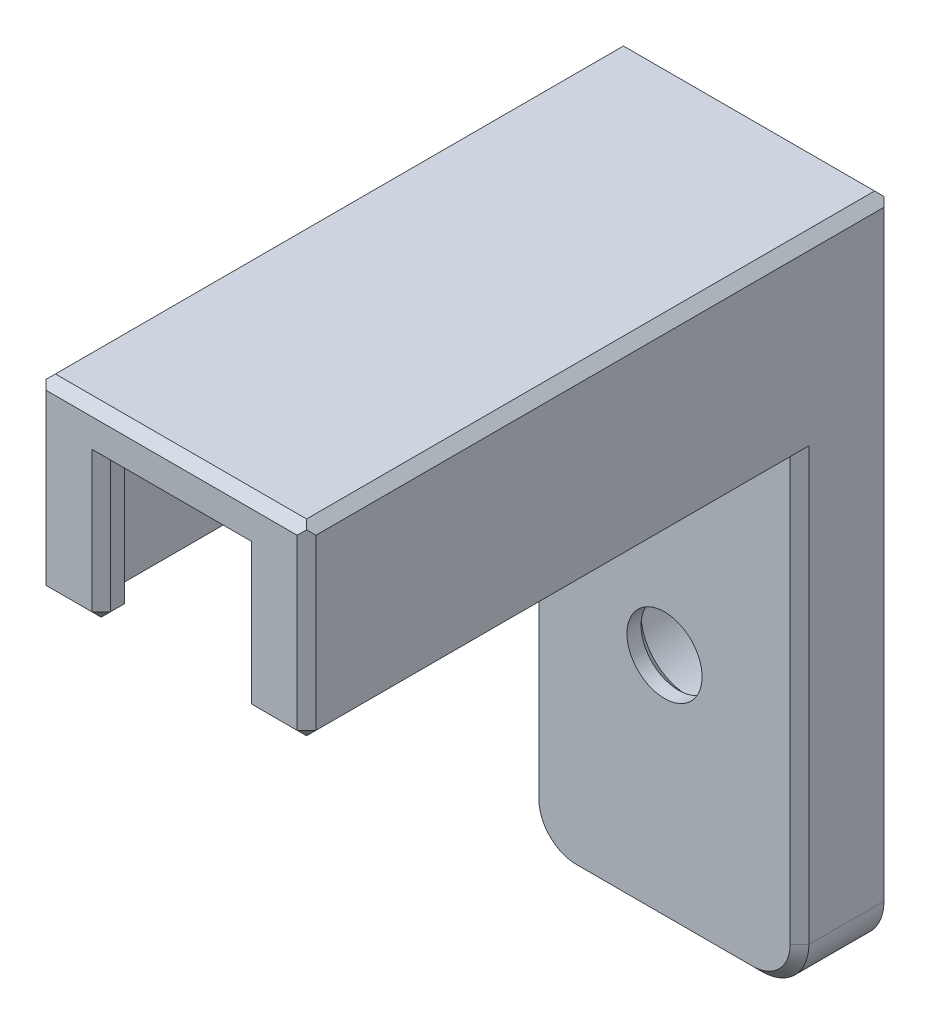
SolidWorks part; units mm, degrees
ref_plane "Front Plane" through (0, 0, 0) normal (0, 0, 1) x (1, 0, 0)
ref_plane "Top Plane" through (0, 0, 0) normal (0, 1, 0) x (1, 0, 0)
ref_plane "Right Plane" through (0, 0, 0) normal (1, 0, 0) x (0, 0, -1)
sketch "Sketch1" plane through (0, 0, 0) normal (0, 1, 0) x (1, 0, 0)
  line L1 (-5.75, 12.5) -> (5.75, 12.5)
  line L2 (-5.75, 12.5) -> (-5.75, -12.5)
  line L3 (-5.75, -12.5) -> (5.75, -12.5)
  line L4 (5.75, 12.5) -> (5.75, -12.5)
  point P4 (0, -12.5)
  point P6 (-5.75, 0)
  dimension "D1" = 25
  dimension "D2" = 11.5
extrude "Boss-Extrude1" add sketch "Sketch1" along normal blind 8
sketch "Sketch2" plane through (0, 0, 0) normal (0, -1, 0) x (1, 0, 0)
  line L0 (-5.75, 12.5) -> (5.75, 12.5) construction
  line L1 (-3, 12.5) -> (3, 12.5)
  line L2 (-3, 12.5) -> (-3, 11.5)
  line L4 (3, 12.5) -> (3, 11.5)
  line L5 (3, 11.5) -> (3.8, 11.5)
  line L6 (-3.8, 11.5) -> (-3, 11.5)
  line L7 (-3.8, 11.5) -> (-3.8, 4.5)
  line L8 (-3.8, 4.5) -> (-3, 4.5)
  line L9 (3.8, 11.5) -> (3.8, 4.5)
  line L10 (-3, 11.5) -> (3, 11.5) construction
  line L12 (3, 4.5) -> (3.8, 4.5)
  line L13 (-3, 4.5) -> (3, 4.5) construction
  line L14 (-3, 4.5) -> (-3, -2.5)
  line L15 (-3, -2.5) -> (3, -2.5)
  line L16 (3, 4.5) -> (3, -2.5)
  line L17 (-3, 4.5) -> (3, 4.5) construction
  point P10 (0, 12.5)
  point P13 (3.4, 11.5)
  dimension "D1" = 7.6
  dimension "D2" = 6
  dimension "D3" = 1
  dimension "D4" = 7
  dimension "D5" = 6
  dimension "D6" = 14
extrude "Cut-Extrude1" cut sketch "Sketch2" against normal offset from surface (6 mm away) 6 up to face at (0, 0, 0)
sketch "Sketch3" plane through (0, 0, 0) normal (0, -1, 0) x (1, 0, 0)
  line L0 (5.75, 12.5) -> (5.75, -12.5) construction
  line L1 (-5.75, -12.5) -> (5.75, -12.5)
  line L2 (-5.75, -12.5) -> (-5.75, -8.5)
  line L3 (-5.75, -8.5) -> (5.75, -8.5)
  line L4 (5.75, -12.5) -> (5.75, -8.5)
  line L5 (3.8, 11.5) -> (3, 11.5) construction
  dimension "D1" = 20
extrude "Boss-Extrude2" add sketch "Sketch3" along normal blind 20
hole_wizard "CBORE for M3 SHCS1" positions "Sketch4" profile "Sketch5" counterbore size "M3" standard "ANSI Metric" end condition through all
sketch "Sketch4" plane through (0, 0, -12.5) normal (0, 0, -1) x (-1, 0, 0)
  line L0 (5.75, -20) -> (-5.75, -20) construction
  point P0 (0, -10)
  point P5 (0, 0)
  point P6 (0, -20)
  dimension "D1" = 10
sketch "Sketch5" plane through (0, -10, -12.5) normal (1, 0, 0) x (0, 1, 0)
  line L0 (0, 0) -> (0, 25)
  line L1 (0, 25) -> (1.6, 25)
  line L3 (1.6, 25) -> (1.6, 3)
  line L4 (1.6, 3) -> (3.3, 3)
  line L5 (3.3, 3) -> (3.3, 0)
  line L7 (3.3, 0) -> (0, 0)
  line L11 (0, -6.35) -> (0, 107.95) construction
  dimension "Thru Hole Dia." = 3.2
  dimension "Thru Hole Depth" = 25
  dimension "C'Bore Dia." = 6.6
  dimension "C'Bore Depth" = 3
fillet "Fillet1" radius 2 2 edges at (-5.75, -20, -10.5) (5.75, -20, -10.5)
chamfer "Chamfer1" distance 0.4 angle 45 4 edges at (0, 8, -12.5) (5.75, 8, 0) (0, 8, 12.5) (-5.75, 8, 0)
chamfer "Chamfer2" distance 0.4 angle 45 32 edges at (-5.75, -9, -8.5) (-5.1642, -19.4142, -8.5) (0, -20, -8.5) (5.1642, -19.4142, -8.5) (5.75, -9, -8.5) (5.75, 3.8, 12.5) (4.375, 0, 12.5) (-3, 3, 12.5) (0, 6, 12.5) (3, 3, 12.5) (3, 0, 12) (3.4, 0, 11.5) (3.8, 0, 8) (3.4, 0, 4.5) (3, 0, 1) (0, 0, -2.5) (-3, 0, 1) (-3.4, 0, 4.5) (-3.8, 0, 8) (-3.4, 0, 11.5) (-3, 0, 12) (-4.375, 0, 12.5) (-5.75, 0, 2) (-5.75, 3.8, 12.5) (-1.6, -10, -9.5) (-3.3, -10, -12.5) (5.75, -5.2, -12.5) (5.1642, -19.4142, -12.5) (0, -20, -12.5) (-5.1642, -19.4142, -12.5) (-5.75, -5.2, -12.5) (5.75, 0, 2)
